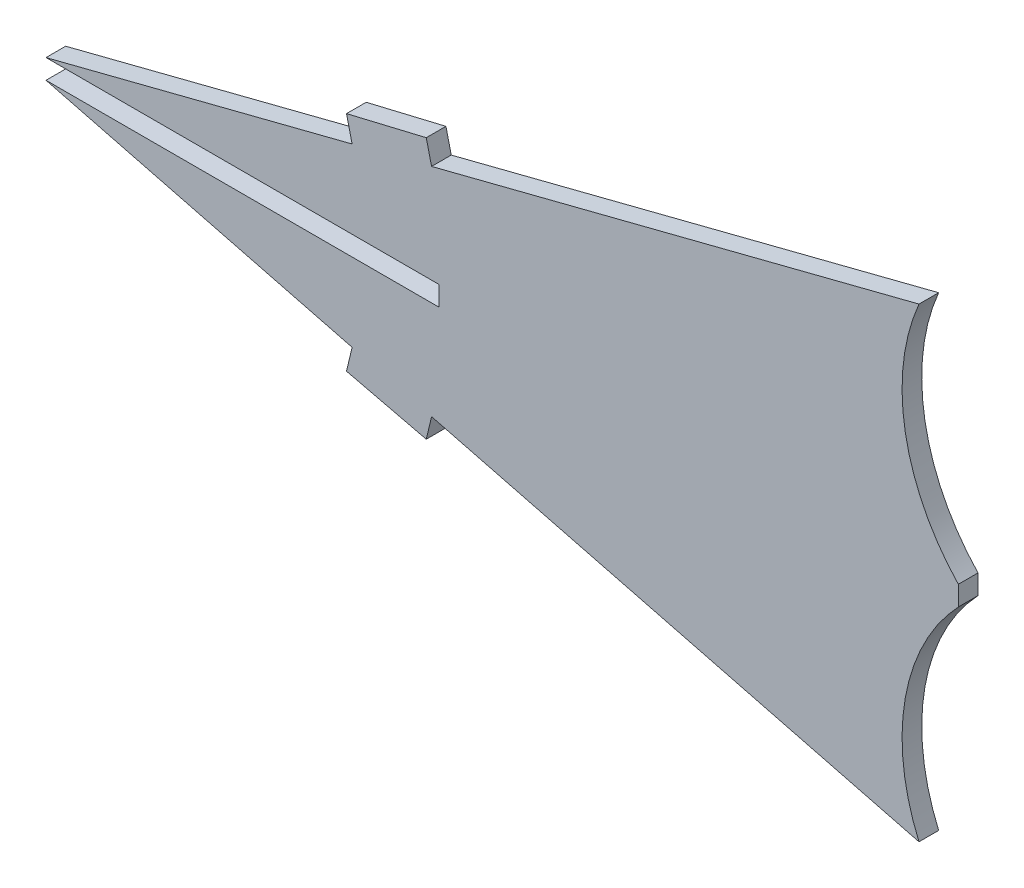
SolidWorks part; units mm, degrees
ref_plane "Front Plane" through (0, 0, 0) normal (0, 0, 1) x (1, 0, 0)
ref_plane "Top Plane" through (0, 0, 0) normal (0, 1, 0) x (1, 0, 0)
ref_plane "Right Plane" through (0, 0, 0) normal (1, 0, 0) x (0, 0, -1)
sketch "Sketch1" plane through (0, 0, 0) normal (0, 0, 1) x (1, 0, 0)
  line L0 (150.0367, -1.524) -> (150.0367, 0)
  line L1 (164.3276, -0.762) -> (183.967, -0.762) construction
  line L2 (190.2622, 0) -> (190.2622, -1.524)
  line L5 (119.6056, -1.524) -> (143.3139, -7.5806)
  line L6 (119.6056, -1.524) -> (150.0367, -1.524)
  line L7 (149.4671, 7.6286) -> (187.2154, 17.272)
  line L8 (143.3139, -7.5806) -> (142.8795, -9.4012)
  line L9 (149.4671, -9.1526) -> (149.0561, -10.8749)
  line L10 (142.8795, 7.8772) -> (149.0561, 9.3509)
  line L11 (142.8795, -9.4012) -> (149.0561, -10.8749)
  line L12 (149.4671, -9.1526) -> (187.2154, -18.796)
  line L13 (149.4671, 7.6286) -> (149.0561, 9.3509)
  line L14 (143.3139, 6.0566) -> (142.8795, 7.8772)
  line L15 (119.6056, 0) -> (150.0367, 0)
  line L16 (119.6056, 0) -> (143.3139, 6.0566)
  line L19 (192.2574, -1.524) -> (150.0367, -1.524) construction
  arc A0 (187.2154, -18.796) -> (190.2622, -1.524) centre (201.8304, -12.4694) cw
  arc A1 (187.2154, 17.272) -> (190.2622, 0) centre (201.8304, 10.9454) ccw
  point P4 (156.0179, -4.0539)
  point P12 (154.4764, -10.5146)
  point P15 (157.5003, -4.4076)
  point P16 (155.9588, -10.8683)
  point P17 (167.7502, -8.4198)
  point P18 (145.0606, -3.0064)
extrude "Boss-Extrude1" add sketch "Sketch1" along normal blind 1.524
